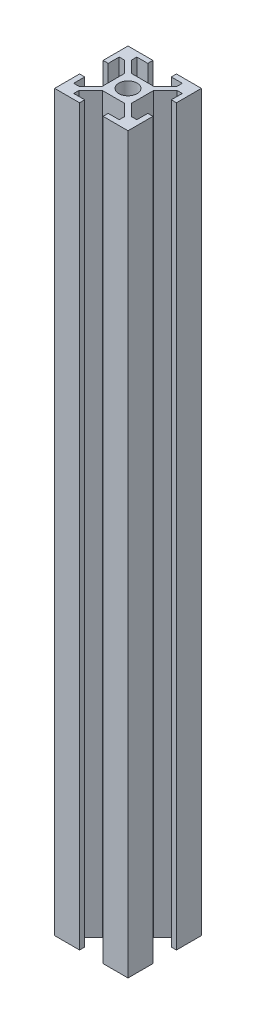
SolidWorks part; units mm, degrees
ref_plane "Front Plane" through (0, 0, 0) normal (0, 0, 1) x (1, 0, 0)
ref_plane "Top Plane" through (0, 0, 0) normal (0, 1, 0) x (1, 0, 0)
ref_plane "Right Plane" through (0, 0, 0) normal (1, 0, 0) x (0, 0, -1)
sketch "Sketch1" plane through (0, 0, 0) normal (0, 1, 0) x (1, 0, 0)
  line L0 (-3.2, 10) -> (-3.2, 8.6)
  line L1 (-10, -10) -> (-3.2, -10)
  line L2 (-10, -10) -> (-10, -3.2)
  line L3 (-10, 10) -> (-3.2, 10)
  line L4 (10, -10) -> (10, -3.2)
  line L5 (-10, -10) -> (10, 10) construction
  line L6 (-10, 10) -> (10, -10) construction
  line L7 (-6.2, 7.1899) -> (-3, 3.9899)
  line L8 (-3, 3.9899) -> (3, 3.9899)
  line L9 (-3.2, 8.6) -> (-6.2, 8.6)
  line L10 (-6.2, 8.6) -> (-6.2, 7.1899)
  line L11 (0, 0) -> (0, 11.8092) construction
  line L12 (3.2, 10) -> (10, 10)
  line L13 (6.2, 7.1899) -> (3, 3.9899)
  line L14 (6.2, 8.6) -> (6.2, 7.1899)
  line L15 (3.2, 8.6) -> (6.2, 8.6)
  line L16 (3.2, 10) -> (3.2, 8.6)
  line L17 (3.9899, -3) -> (3.9899, 3)
  line L18 (8.6, -6.2) -> (7.1899, -6.2)
  line L19 (7.1899, -6.2) -> (3.9899, -3)
  line L20 (8.6, -3.2) -> (8.6, -6.2)
  line L21 (7.1899, 6.2) -> (3.9899, 3)
  line L22 (8.6, 6.2) -> (7.1899, 6.2)
  line L23 (8.6, 3.2) -> (8.6, 6.2)
  line L24 (10, 3.2) -> (8.6, 3.2)
  line L25 (10, -3.2) -> (8.6, -3.2)
  line L26 (-10, -3.2) -> (-8.6, -3.2)
  line L27 (-8.6, -3.2) -> (-8.6, -6.2)
  line L28 (-8.6, -6.2) -> (-7.1899, -6.2)
  line L29 (-7.1899, -6.2) -> (-3.9899, -3)
  line L30 (-8.6, 6.2) -> (-7.1899, 6.2)
  line L31 (-8.6, 3.2) -> (-8.6, 6.2)
  line L32 (-3.9899, 3) -> (-3.9899, -3)
  line L33 (-7.1899, 6.2) -> (-3.9899, 3)
  line L34 (-10, 3.2) -> (-8.6, 3.2)
  line L35 (3.2, -10) -> (3.2, -8.6)
  line L36 (6.2, -7.1899) -> (3, -3.9899)
  line L37 (3, -3.9899) -> (-3, -3.9899)
  line L38 (3.2, -8.6) -> (6.2, -8.6)
  line L39 (6.2, -8.6) -> (6.2, -7.1899)
  line L40 (-6.2, -7.1899) -> (-3, -3.9899)
  line L41 (-6.2, -8.6) -> (-6.2, -7.1899)
  line L42 (-3.2, -8.6) -> (-6.2, -8.6)
  line L43 (-3.2, -10) -> (-3.2, -8.6)
  line L44 (10, 3.2) -> (10, 10)
  line L45 (-10, 3.2) -> (-10, 10)
  line L46 (3.2, -10) -> (10, -10)
  circle A0 centre (0, 0) radius 2.5
  point P0 (0, 0)
  point P17 (0, 3.9899)
  point P40 (-3.9899, 0)
  point P51 (0, -3.9899)
  dimension "D1" = 5
  dimension "D2" = 20
  dimension "D3" = 3.2
  dimension "D4" = 1.4
  dimension "D5" = 0.7
  dimension "D6" = 3
  dimension "D7" = 3
extrude "Boss-Extrude1" add sketch "Sketch1" along normal blind 200
